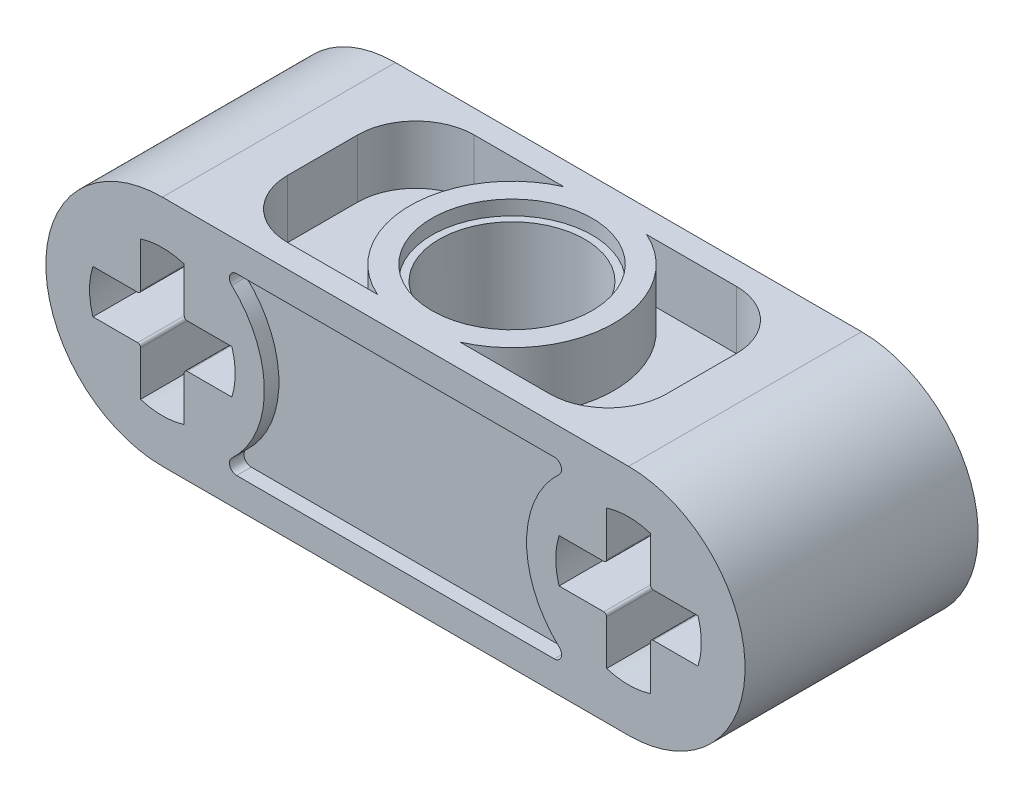
SolidWorks part; units mm, degrees
ref_plane "Alzado" through (0, 0, 0) normal (0, 0, 1) x (1, 0, 0)
ref_plane "Planta" through (0, 0, 0) normal (0, 1, 0) x (1, 0, 0)
ref_plane "Vista lateral" through (0, 0, 0) normal (1, 0, 0) x (0, 0, -1)
sketch "Croquis1" plane through (0, 0, 0) normal (0, 0, 1) x (1, 0, 0)
  line L0 (0, 0) -> (19.4732, 0) construction
  line L1 (0, 0) -> (0, 10.1136) construction
  line L2 (-8, 4) -> (8, 4)
  line L3 (-8, -4) -> (8, -4)
  line L4 (8, 0) -> (8, -3.2227) construction
  line L5 (10.3848, -0.75) -> (8.85, -0.75)
  line L6 (8.75, -0.85) -> (8.75, -2.3848)
  line L7 (7.25, -0.85) -> (7.25, -2.3848)
  line L8 (5.6152, -0.75) -> (7.15, -0.75)
  line L9 (5.6152, 0.75) -> (7.15, 0.75)
  line L10 (7.25, 0.85) -> (7.25, 2.3848)
  line L11 (8.75, 0.85) -> (8.75, 2.3848)
  line L12 (10.3848, 0.75) -> (8.85, 0.75)
  line L13 (-10.3848, 0.75) -> (-8.85, 0.75)
  line L14 (-8.75, 0.85) -> (-8.75, 2.3848)
  line L15 (-7.25, 0.85) -> (-7.25, 2.3848)
  line L16 (-5.6152, 0.75) -> (-7.15, 0.75)
  line L17 (-5.6152, -0.75) -> (-7.15, -0.75)
  line L18 (-7.25, -0.85) -> (-7.25, -2.3848)
  line L19 (-8.75, -0.85) -> (-8.75, -2.3848)
  line L20 (-10.3848, -0.75) -> (-8.85, -0.75)
  arc A0 (8, -4) -> (8, 4) centre (8, 0) ccw
  arc A1 (-8, -4) -> (-8, 4) centre (-8, 0) cw
  arc A2 (10.3848, 0.75) -> (10.3848, -0.75) centre (8, 0) cw
  arc A3 (8.75, -2.3848) -> (7.25, -2.3848) centre (8, 0) cw
  arc A4 (8.85, -0.75) -> (8.75, -0.85) centre (8.85, -0.85) ccw
  arc A5 (7.15, -0.75) -> (7.25, -0.85) centre (7.15, -0.85) cw
  arc A6 (5.6152, 0.75) -> (5.6152, -0.75) centre (8, 0) ccw
  arc A7 (7.15, 0.75) -> (7.25, 0.85) centre (7.15, 0.85) ccw
  arc A8 (8.85, 0.75) -> (8.75, 0.85) centre (8.85, 0.85) cw
  arc A9 (8.75, 2.3848) -> (7.25, 2.3848) centre (8, 0) ccw
  arc A10 (-8.75, 2.3848) -> (-7.25, 2.3848) centre (-8, 0) cw
  arc A11 (-8.85, 0.75) -> (-8.75, 0.85) centre (-8.85, 0.85) ccw
  arc A12 (-7.15, 0.75) -> (-7.25, 0.85) centre (-7.15, 0.85) cw
  arc A13 (-5.6152, 0.75) -> (-5.6152, -0.75) centre (-8, 0) cw
  arc A14 (-7.15, -0.75) -> (-7.25, -0.85) centre (-7.15, -0.85) ccw
  arc A15 (-8.85, -0.75) -> (-8.75, -0.85) centre (-8.85, -0.85) cw
  arc A16 (-8.75, -2.3848) -> (-7.25, -2.3848) centre (-8, 0) ccw
  arc A17 (-10.3848, 0.75) -> (-10.3848, -0.75) centre (-8, 0) ccw
  point P4 (0, -4)
  point P11 (0, 4)
  dimension "D3" = 2.5
  dimension "D6" = 0.1
  dimension "D1" = 16
  dimension "D2" = 8
  dimension "D4" = 1.5
  dimension "D5" = 1.5
extrude "Extruir1" add sketch "Croquis1" along normal mid plane 8
sketch "Croquis2" plane through (0, 4, 0) normal (0, 1, 0) x (-1, 0, 0)
  circle A0 centre (0, 0) radius 2.5
  dimension "D1" = 5
extrude "Cortar-Extruir1" cut sketch "Croquis2" against normal through all
sketch "Croquis3" plane through (0, 4, 0) normal (0, 1, 0) x (-1, 0, 0)
  circle A0 centre (0, 0) radius 2.75
  dimension "D1" = 5.5
extrude "Cortar-Extruir2" cut sketch "Croquis3" against normal blind 0.5
mirror "Simetría1" about plane through (0, 0, 0) normal (0, 1, 0) of "Cortar-Extruir2"
sketch "Croquis4" plane through (0, 4, 0) normal (0, 1, 0) x (-1, 0, 0)
  line L0 (-1.4177, -3.2) -> (-6.5, -3.2)
  line L1 (-6.5, -3.2) -> (-6.5, 3.2)
  line L2 (-6.5, 3.2) -> (-1.4177, 3.2)
  line L3 (-8, 4) -> (-8, -4) construction
  line L4 (-8, -4) -> (8, -4) construction
  line L5 (-8, 4) -> (8, 4) construction
  arc A0 (-1.4177, -3.2) -> (-1.4177, 3.2) centre (0, 0) cw
  dimension "D1" = 3.5
  dimension "D2" = 1.5
  dimension "D3" = 0.8
  dimension "D4" = 0.8
extrude "Cortar-Extruir3" cut sketch "Croquis4" against normal blind 2
mirror "Simetría2" about plane through (0, 0, 0) normal (1, 0, 0) of "Cortar-Extruir3"
mirror "Simetría3" about plane through (0, 0, 0) normal (0, 1, 0) of "Simetría2", "Cortar-Extruir3"
fillet "Redondeo1" radius 2 8 edges at (-6.5, 3, -3.2) (6.5, -3, -3.2) (6.5, -3, 3.2) (-6.5, -3, -3.2) (-6.5, -3, 3.2) (6.5, 3, -3.2) (6.5, 3, 3.2) (-6.5, 3, 3.2)
sketch "Croquis5" plane through (0, 0, 4) normal (0, 0, 1) x (1, 0, 0)
  line L0 (-8, 0) -> (0, 0) construction
  line L1 (0, 0) -> (0, 4) construction
  line L2 (8, 4) -> (-8, 4) construction
  line L3 (-5.4505, 3) -> (5.4505, 3)
  line L4 (-5.4505, -3) -> (5.4505, -3)
  arc A0 (-5.6205, -2.5667) -> (-5.6205, 2.5667) centre (-8, 0) ccw
  arc A1 (-7.25, 2.3848) -> (-8.75, 2.3848) centre (-8, 0) ccw construction
  arc A2 (-5.6205, 2.5667) -> (-5.4505, 3) centre (-5.4505, 2.75) cw
  arc A3 (5.6205, 2.5667) -> (5.4505, 3) centre (5.4505, 2.75) ccw
  arc A4 (5.6205, -2.5667) -> (5.6205, 2.5667) centre (8, 0) cw
  arc A5 (5.6205, -2.5667) -> (5.4505, -3) centre (5.4505, -2.75) cw
  arc A6 (-5.6205, -2.5667) -> (-5.4505, -3) centre (-5.4505, -2.75) ccw
  point P19 (0, 3)
  point P23 (0, -3)
  dimension "D1" = 0.25
  dimension "D3" = 3.5
  dimension "D2" = 1
extrude "Cortar-Extruir4" cut sketch "Croquis5" against normal blind 0.5
mirror "Simetría4" about plane through (0, 0, 0) normal (0, 0, 1) of "Cortar-Extruir4"
